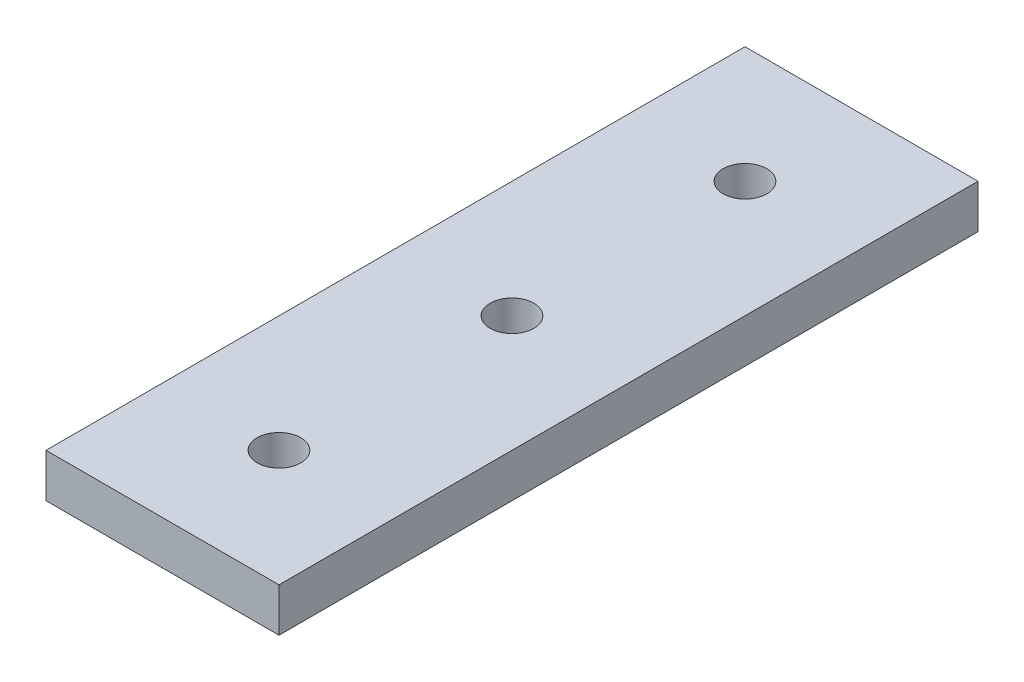
SolidWorks part; units mm, degrees
material "Alloy Steel"
ref_plane "Front Plane" through (0, 0, 0) normal (0, 0, 1) x (1, 0, 0)
ref_plane "Top Plane" through (0, 0, 0) normal (0, 1, 0) x (1, 0, 0)
ref_plane "Right Plane" through (0, 0, 0) normal (1, 0, 0) x (0, 0, -1)
other "Configuration Table"
sketch "Sketch1" plane through (0, 0, 0) normal (0, 1, 0) x (1, 0, 0)
  line L1 (-12.7, 38.1) -> (12.7, 38.1)
  line L2 (-12.7, 38.1) -> (-12.7, -38.1)
  line L3 (-12.7, -38.1) -> (12.7, -38.1)
  line L4 (12.7, 38.1) -> (12.7, -38.1)
  line L5 (-12.7, 38.1) -> (12.7, -38.1) construction
  line L6 (-12.7, -38.1) -> (12.7, 38.1) construction
  point P0 (0, 0)
  dimension "D1" = 76.2
  dimension "D2" = 25.4
extrude "Boss-Extrude1" add sketch "Sketch1" along normal blind 4.7625
sketch "Sketch2" plane through (0, 4.7625, 0) normal (0, 1, 0) x (1, 0, 0)
  line L0 (12.7, 38.1) -> (-12.7, 38.1) construction
  line L1 (-12.7, -38.1) -> (12.7, -38.1) construction
  circle A0 centre (0, 25.4) radius 2.3813
  circle A1 centre (0, 0) radius 2.3813
  circle A2 centre (0, -25.4) radius 2.3813
  dimension "D5" = 4.7625
  dimension "D6" = 4.7625
  dimension "D7" = 4.7625
  dimension "D1" = 25.4
  dimension "D2" = 25.4
  dimension "D3" = 12.7
  dimension "D4" = 12.7
extrude "Cut-Extrude1" cut sketch "Sketch2" against normal through all
